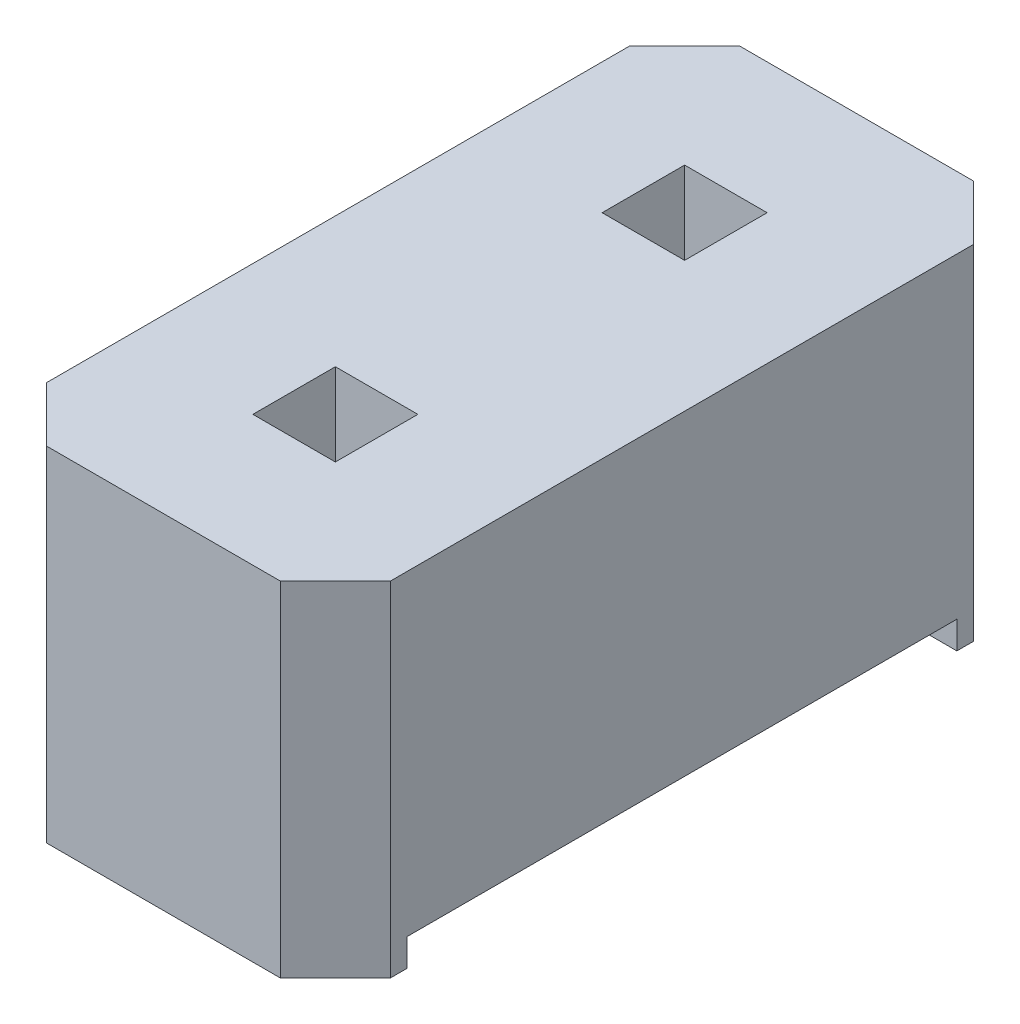
SolidWorks part; units mm, degrees
ref_plane "Plan de face" through (0, 0, 0) normal (0, 0, 1) x (1, 0, 0)
ref_plane "Plan de dessus" through (0, 0, 0) normal (0, 1, 0) x (1, 0, 0)
ref_plane "Plan de droite" through (0, 0, 0) normal (1, 0, 0) x (0, 0, -1)
sketch "Esquisse1" plane through (0, 0, 0) normal (0, 1, 0) x (1, 0, 0)
  line L0 (-1.25, 2.12) -> (-0.85, 2.52)
  line L1 (-0.85, -2.52) -> (0.85, -2.52)
  line L2 (-1.25, -2.12) -> (-1.25, 2.12)
  line L3 (-0.85, 2.52) -> (0.85, 2.52)
  line L4 (1.25, -2.12) -> (1.25, 2.12)
  line L5 (-1.25, -2.52) -> (1.25, 2.52) construction
  line L6 (-1.25, 2.52) -> (1.25, -2.52) construction
  line L7 (0.85, 2.52) -> (1.25, 2.12)
  line L8 (0.85, -2.52) -> (1.25, -2.12)
  line L9 (-1.25, -2.12) -> (-0.85, -2.52)
  line L10 (0.3, -0.97) -> (-0.3, -1.57) construction
  line L11 (0.3, -0.97) -> (-0.3, -0.97)
  line L12 (0.3, -0.97) -> (0.3, -1.57)
  line L13 (0.3, -1.57) -> (-0.3, -1.57)
  line L14 (-0.3, -0.97) -> (-0.3, -1.57)
  line L15 (1.25, 0) -> (-1.25, 0) construction
  line L16 (0.3, 0.97) -> (0.3, 1.57)
  line L17 (0.3, 1.57) -> (-0.3, 1.57)
  line L18 (-0.3, 0.97) -> (-0.3, 1.57)
  line L19 (0.3, 0.97) -> (-0.3, 0.97)
  point P0 (0, 0)
  point P14 (0, 0)
  point P19 (0, -1.27)
  dimension "D1" = 2.5
  dimension "D2" = 5.04
  dimension "D3" = 0.6
  dimension "D4" = 2.54
extrude "Boss.-Extru.1" add sketch "Esquisse1" along normal blind 2.5
sketch "Esquisse2" plane through (-1.25, 0, 0) normal (-1, 0, 0) x (0, 0, 1)
  line L2 (-2, -0.2) -> (2, -0.2)
  line L3 (-2, -0.2) -> (-2, 0.2)
  line L4 (-2, 0.2) -> (2, 0.2)
  line L5 (2, -0.2) -> (2, 0.2)
  line L6 (-2, -0.2) -> (2, 0.2) construction
  line L7 (-2, 0.2) -> (2, -0.2) construction
  point P0 (0, 0)
  dimension "D1" = 0.2
  dimension "D2" = 4
extrude "Enlèv. mat.-Extru.1" cut sketch "Esquisse2" against normal through all
